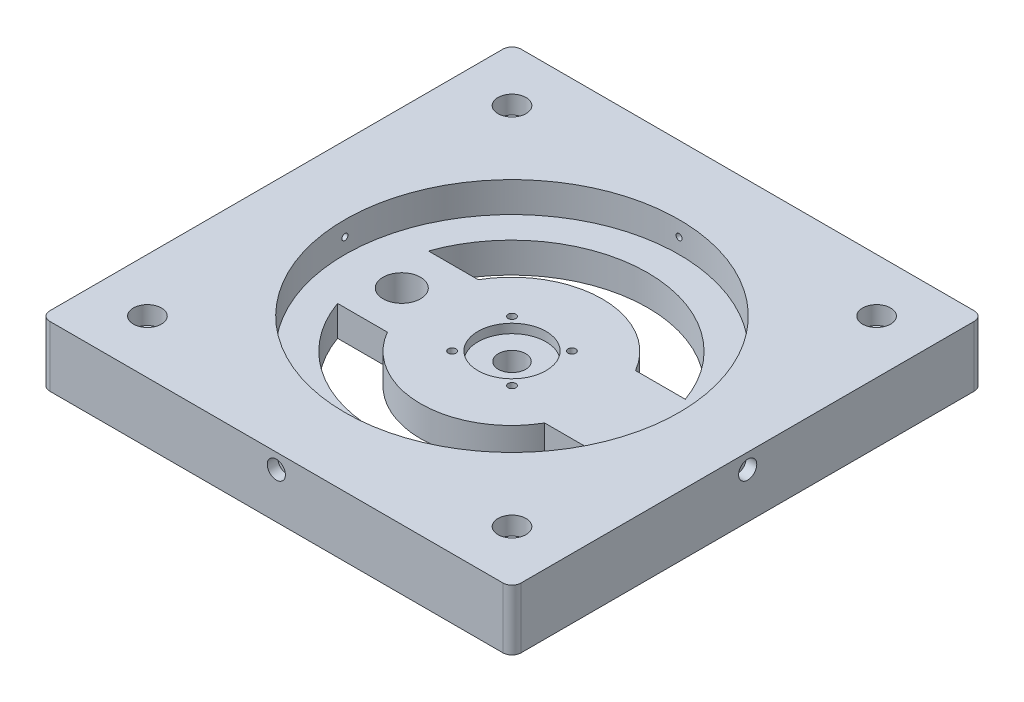
SolidWorks part; units mm, degrees
ref_plane "Front Plane" through (0, 0, 0) normal (0, 0, 1) x (1, 0, 0)
ref_plane "Top Plane" through (0, 0, 0) normal (0, 1, 0) x (1, 0, 0)
ref_plane "Right Plane" through (0, 0, 0) normal (1, 0, 0) x (0, 0, -1)
sketch "Sketch1" plane through (0, 0, 0) normal (0, 1, 0) x (1, 0, 0)
  line L0 (77.4608, -75.0982) -> (77.4608, 74.5774)
  line L1 (74.4472, 77.591) -> (-75.2284, 77.591)
  line L2 (-78.242, 74.5774) -> (-78.242, -75.0982)
  line L3 (-75.2284, -78.1118) -> (74.4472, -78.1118)
  line L4 (-78.242, -0.2604) -> (77.4608, -0.2604) construction
  line L5 (-0.3906, 77.591) -> (-0.3906, -78.1118) construction
  circle A0 centre (-60.6043, -60.4741) radius 2.6376
  circle A1 centre (-60.6043, 59.9534) radius 2.6376
  circle A2 centre (59.8232, 59.9534) radius 2.6376
  circle A3 centre (59.8232, -60.4741) radius 2.6376
  arc A4 (77.4608, 74.5774) -> (74.4472, 77.591) centre (74.4472, 74.5774) ccw
  arc A5 (-75.2284, 77.591) -> (-78.242, 74.5774) centre (-75.2284, 74.5774) ccw
  arc A6 (-78.242, -75.0982) -> (-75.2284, -78.1118) centre (-75.2284, -75.0982) ccw
  arc A7 (74.4472, -78.1118) -> (77.4608, -75.0982) centre (74.4472, -75.0982) ccw
  circle A10 centre (-0.3906, -0.2604) radius 73
  dimension "D2" = 146
  dimension "D1" = 155.7028
extrude "Boss-Extrude1" add sketch "Sketch1" along normal blind 20
sketch "Sketch7" plane through (0, 20, 0) normal (0, 1, 0) x (1, 0, 0)
  circle A0 centre (-0.3906, -0.2604) radius 73 construction
  circle A1 centre (-0.3906, -0.2604) radius 73
  circle A2 centre (-0.3906, -0.2604) radius 52.25
  dimension "D1" = 104.5
extrude "Boss-Extrude2" add sketch "Sketch7" against normal blind 10
sketch "Sketch8" plane through (0, 10, 0) normal (0, -1, 0) x (1, 0, 0)
  circle A1 centre (-0.3906, 0.2604) radius 73
  circle A2 centre (-0.3906, 0.2604) radius 73
  dimension "D1" = 0
extrude "Boss-Extrude3" add sketch "Sketch8" along normal up to surface (10 mm away) up to face at (-0.3906, 0, 0.2604)
sketch "Sketch9" plane through (0, 10, 0) normal (0, 1, 0) x (1, 0, 0)
  circle A1 centre (-0.3906, -0.2604) radius 11.25
extrude "Cut-Extrude1" cut sketch "Sketch9" against normal blind 3
sketch "Sketch10" plane through (0, 10, 0) normal (0, 1, 0) x (1, 0, 0)
  arc A1 (9.5089, -11.4244) -> (9.5089, -8.8954) centre (9.5089, -10.1599) ccw
  arc A2 (9.5089, -8.8954) -> (9.5089, -11.4244) centre (9.5089, -10.1599) ccw
  arc A3 (-10.2901, -11.4244) -> (-10.2901, -8.8954) centre (-10.2901, -10.1599) ccw
  arc A4 (-10.2901, -8.8954) -> (-10.2901, -11.4244) centre (-10.2901, -10.1599) ccw
  arc A5 (-10.2901, 10.9036) -> (-10.2901, 8.3746) centre (-10.2901, 9.6391) ccw
  arc A6 (-10.2901, 8.3746) -> (-10.2901, 10.9036) centre (-10.2901, 9.6391) ccw
  arc A7 (9.5089, 10.9036) -> (9.5089, 8.3746) centre (9.5089, 9.6391) ccw
  arc A8 (9.5089, 8.3746) -> (9.5089, 10.9036) centre (9.5089, 9.6391) ccw
  circle A11 centre (-0.3906, -0.2604) radius 4.5
extrude "Cut-Extrude2" cut sketch "Sketch10" against normal blind 89
sketch "Sketch11" plane through (0, 20, 0) normal (0, 1, 0) x (1, 0, 0)
  circle A0 centre (-0.3906, -0.2604) radius 52.25 construction
  circle A1 centre (-0.3906, -0.2604) radius 52.25
  circle A2 centre (-0.3906, -0.2604) radius 55.2
  dimension "D1" = 110.4
extrude "Cut-Extrude3" cut sketch "Sketch11" against normal blind 10
sketch "Sketch12" plane through (0, 0, -77.591) normal (0, 0, -1) x (-1, 0, 0)
  line L0 (0.3906, 20) -> (0.3906, 10) construction
  line L1 (-74.4472, 20) -> (75.2284, 20) construction
  circle A0 centre (0.3906, 15) radius 1
  dimension "D2" = 2
  dimension "D1" = 10
extrude "Cut-Extrude4" cut sketch "Sketch12" against normal blind 224
sketch "Sketch13" plane through (-78.242, 0, 0) normal (-1, 0, 0) x (0, 0, 1)
  line L0 (0.2604, 20) -> (0.2604, 10) construction
  line L1 (-74.5774, 20) -> (75.0982, 20) construction
  circle A0 centre (0.2604, 15) radius 1
  dimension "D2" = 2
  dimension "D1" = 10
extrude "Cut-Extrude5" cut sketch "Sketch13" against normal blind 224
sketch "Sketch14" plane through (0, 20, 0) normal (0, 1, 0) x (1, 0, 0)
  circle A0 centre (59.8232, -60.4741) radius 2.6376 construction
  circle A1 centre (-60.6043, -60.4741) radius 2.6376 construction
  circle A2 centre (-60.6043, 59.9534) radius 2.6376 construction
  circle A3 centre (59.8232, 59.9534) radius 2.6376 construction
  circle A4 centre (59.8232, -60.4741) radius 2.6376
  circle A5 centre (-60.6043, -60.4741) radius 2.6376
  circle A6 centre (-60.6043, 59.9534) radius 2.6376
  circle A7 centre (59.8232, 59.9534) radius 2.6376
  circle A8 centre (59.8232, -60.4741) radius 1.6376
  circle A9 centre (-60.6043, -60.4741) radius 1.6376
  circle A10 centre (-60.6043, 59.9534) radius 1.6376
  circle A11 centre (59.8232, 59.9534) radius 1.6376
  dimension "D1" = 1
extrude "Boss-Extrude4" add sketch "Sketch14" against normal up to surface (20 mm away) up to face at (9.5089, 0, -8.3746)
sketch "Sketch16" plane through (0, 20, 0) normal (0, 1, 0) x (1, 0, 0)
  circle A0 centre (59.8232, -60.4741) radius 1.6376 construction
  circle A1 centre (-60.6043, -60.4741) radius 1.6376 construction
  circle A2 centre (-60.6043, 59.9534) radius 1.6376 construction
  circle A3 centre (59.8232, 59.9534) radius 1.6376 construction
  circle A4 centre (59.8232, -60.4741) radius 1.6376
  circle A5 centre (-60.6043, -60.4741) radius 1.6376
  circle A6 centre (-60.6043, 59.9534) radius 1.6376
  circle A7 centre (59.8232, 59.9534) radius 1.6376
  circle A8 centre (59.8232, -60.4741) radius 4.6376
  circle A9 centre (-60.6043, -60.4741) radius 4.6376
  circle A10 centre (-60.6043, 59.9534) radius 4.6376
  circle A11 centre (59.8232, 59.9534) radius 4.6376
  dimension "D1" = 3
extrude "Cut-Extrude7" cut sketch "Sketch16" against normal blind 6
sketch "Sketch17" plane through (0, 10, 0) normal (0, 1, 0) x (1, 0, 0)
  line L1 (-42.817, 14.5496) -> (42.0358, 14.5496)
  line L3 (-42.817, -15.4504) -> (42.0358, -15.4504)
  line L5 (-0.3906, -15.4504) -> (-0.3906, 14.5496) construction
  line L6 (-30.3906, -0.4504) -> (29.6094, -0.4504) construction
  circle A2 centre (-0.3906, -0.4504) radius 30
  circle A3 centre (-0.3906, -0.4504) radius 45
  dimension "D1" = 60
  dimension "D3" = 15
  dimension "D4" = 15
  dimension "D2" = 15
extrude "Cut-Extrude11" cut sketch "Sketch17" against normal blind 15.5 contours L1 A3 A2 | L3 A3 A2
sketch "Sketch18" plane through (0, 0, 0) normal (0, -1, 0) x (1, 0, 0)
  circle A0 centre (-0.3906, 0.2604) radius 4.5 construction
  circle A1 centre (-0.3906, 0.2604) radius 4.5
sketch "Sketch19" plane through (0, 10, 0) normal (0, 1, 0) x (1, 0, 0)
  line L0 (-42.817, 14.5496) -> (-42.817, -15.4504) construction
  line L1 (-42.817, -15.4504) -> (-34.5941, -15.4504) construction
  line L2 (-42.817, -15.4504) -> (-26.3713, -15.4504) construction
  line L3 (-34.5941, -15.4504) -> (-34.5941, 14.5496) construction
  line L4 (-42.817, 14.5496) -> (-26.3713, 14.5496) construction
  line L5 (-34.5941, -0.4504) -> (-42.817, -0.4504) construction
  circle A0 centre (-36.6105, -0.4504) radius 6.2
  dimension "D1" = 12.4
extrude "Cut-Extrude12" cut sketch "Sketch19" against normal blind 144
sketch "Sketch20" plane through (-78.242, 0, 0) normal (-1, 0, 0) x (0, 0, 1)
  circle A0 centre (0.2604, 15) radius 1 construction
  circle A1 centre (0.2604, 15) radius 1
  circle A2 centre (0.2604, 15) radius 3
  dimension "D1" = 6
extrude "Cut-Extrude13" cut sketch "Sketch20" against normal blind 3.5
sketch "Sketch21" plane through (0, 0, 78.1118) normal (0, 0, 1) x (1, 0, 0)
  circle A1 centre (-0.3906, 15) radius 3
  dimension "D1" = 6
extrude "Cut-Extrude14" cut sketch "Sketch21" against normal blind 3.5
sketch "Sketch22" plane through (77.4608, 0, 0) normal (1, 0, 0) x (0, 0, -1)
  circle A0 centre (-0.2604, 15) radius 1 construction
  circle A1 centre (-0.2604, 15) radius 1
  circle A2 centre (-0.2604, 15) radius 3
  dimension "D1" = 6
extrude "Cut-Extrude15" cut sketch "Sketch22" against normal blind 3.5
sketch "Sketch23" plane through (0, 0, -77.591) normal (0, 0, -1) x (-1, 0, 0)
  circle A0 centre (0.3906, 15) radius 3
  dimension "D1" = 6
extrude "Cut-Extrude16" cut sketch "Sketch23" against normal blind 3.5
sketch "Sketch24" plane through (0, 0, 0) normal (0, -1, 0) x (1, 0, 0)
  arc A0 (42.0358, 15.4504) -> (-42.817, 15.4504) centre (-0.3906, 0.4504) ccw construction
  arc A1 (42.0358, 15.4504) -> (-42.817, 15.4504) centre (-0.3906, 0.4504) ccw
  circle A2 centre (-0.3906, 0.4504) radius 45
